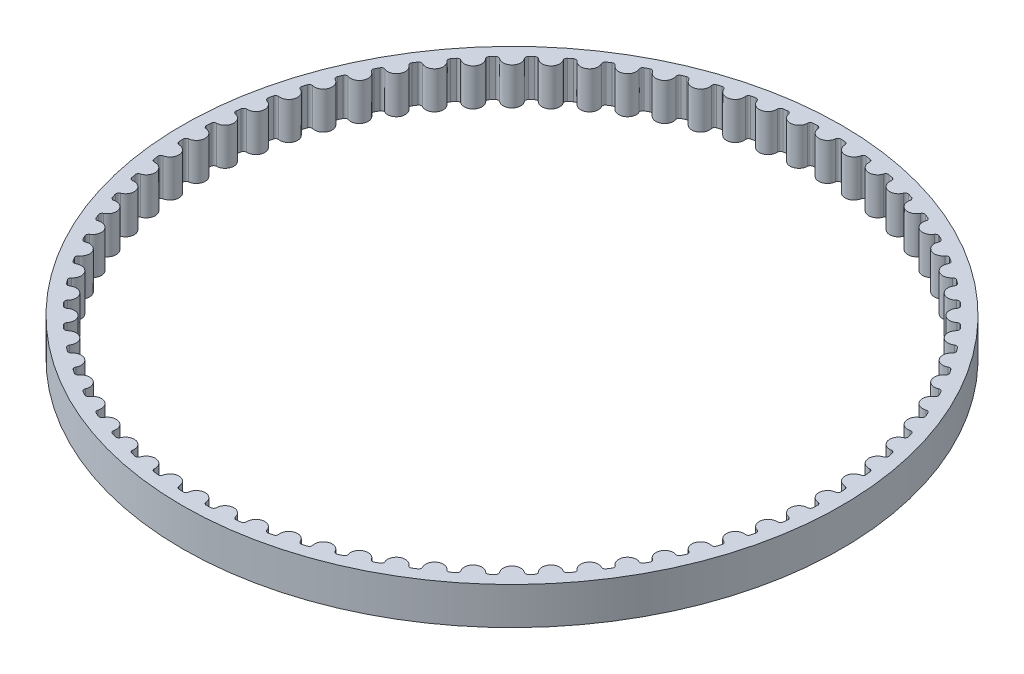
SolidWorks part; units mm, degrees
ref_plane "Front Plane" through (0, 0, 0) normal (0, 0, 1) x (1, 0, 0)
ref_plane "Top Plane" through (0, 0, 0) normal (0, 1, 0) x (1, 0, 0)
ref_plane "Right Plane" through (0, 0, 0) normal (1, 0, 0) x (0, 0, -1)
sketch "Sketch1" plane through (0, 0, 0) normal (0, 1, 0) x (1, 0, 0)
  circle A0 centre (0, 0) radius 35.2965
  arc B0 (-1.7184, -33.953) -> (-1.2474, -33.9736) centre (0, 0) ccw
  arc B1 (-1.2474, -33.9736) -> (-0.9391, -33.7063) centre (-1.2364, -33.6748) ccw
  arc B2 (0.9391, -33.7063) -> (-0.9391, -33.7063) centre (0, -33.806) ccw
  arc B3 (0.9391, -33.7063) -> (1.2474, -33.9736) centre (1.2364, -33.6748) ccw
  arc B4 (1.2474, -33.9736) -> (1.7184, -33.953) centre (0, 0) ccw
  arc B5 (1.7184, -33.953) -> (2.0022, -33.6599) centre (1.7032, -33.6544) ccw
  arc B6 (3.8732, -33.4962) -> (2.0022, -33.6599) centre (2.9464, -33.6773) ccw
  arc B7 (3.8732, -33.4962) -> (4.2036, -33.7356) centre (4.1667, -33.4389) ccw
  arc B8 (4.2036, -33.7356) -> (4.671, -33.674) centre (0, 0) ccw
  arc B9 (4.671, -33.674) -> (4.9282, -33.3573) centre (4.6299, -33.3779) ccw
  arc B10 (6.7779, -33.0312) -> (4.9282, -33.3573) centre (5.8703, -33.2924) ccw
  arc B11 (6.7779, -33.0312) -> (7.1279, -33.2408) centre (7.0652, -32.9485) ccw
  arc B12 (7.1279, -33.2408) -> (7.5881, -33.1388) centre (0, 0) ccw
  arc B13 (7.5881, -33.1388) -> (7.8168, -32.8009) centre (7.5214, -32.8473) ccw
  arc B14 (9.6309, -32.3148) -> (7.8168, -32.8009) centre (8.7496, -32.6541) ccw
  arc B15 (9.6309, -32.3148) -> (9.9979, -32.4931) centre (9.9099, -32.2073) ccw
  arc B16 (9.9979, -32.4931) -> (10.4475, -32.3513) centre (0, 0) ccw
  arc B17 (10.4475, -32.3513) -> (10.6458, -31.9948) centre (10.3556, -32.0668) ccw
  arc B18 (12.4107, -31.3524) -> (10.6458, -31.9948) centre (11.5623, -31.7672) ccw
  arc B19 (12.4107, -31.3524) -> (12.7918, -31.4981) centre (12.6793, -31.2211) ccw
  arc B20 (12.7918, -31.4981) -> (13.2273, -31.3177) centre (0, 0) ccw
  arc B21 (13.2273, -31.3177) -> (13.3938, -30.9452) centre (13.111, -31.0422) ccw
  arc B22 (15.096, -30.1514) -> (13.3938, -30.9452) centre (14.287, -30.6386) ccw
  arc B23 (15.096, -30.1514) -> (15.4884, -30.2634) centre (15.3521, -29.9972) ccw
  arc B24 (15.4884, -30.2634) -> (15.9065, -30.0457) centre (0, 0) ccw
  arc B25 (15.9065, -30.0457) -> (16.0399, -29.6601) centre (15.7666, -29.7814) ccw
  arc B26 (17.6664, -28.721) -> (16.0399, -29.6601) centre (16.903, -29.2768) ccw
  arc B27 (17.6664, -28.721) -> (18.067, -28.7983) centre (17.9081, -28.545) ccw
  arc B28 (18.067, -28.7983) -> (18.4647, -28.545) centre (0, 0) ccw
  arc B29 (18.4647, -28.545) -> (18.5639, -28.1492) centre (18.3023, -28.2939) ccw
  arc B30 (20.1024, -27.072) -> (18.5639, -28.1492) centre (19.3903, -27.6922) ccw
  arc B31 (20.1024, -27.072) -> (20.5082, -27.1141) centre (20.3279, -26.8756) ccw
  arc B32 (20.5082, -27.1141) -> (20.8822, -26.8271) centre (0, 0) ccw
  arc B33 (20.8822, -26.8271) -> (20.9466, -26.4242) centre (20.6986, -26.5911) ccw
  arc B34 (22.3854, -25.2169) -> (20.9466, -26.4242) centre (21.7301, -25.8969) ccw
  arc B35 (22.3854, -25.2169) -> (22.7933, -25.2235) centre (22.5929, -25.0016) ccw
  arc B36 (22.7933, -25.2235) -> (23.1409, -24.905) centre (0, 0) ccw
  arc B37 (23.1409, -24.905) -> (23.1699, -24.498) centre (22.9374, -24.6859) ccw
  arc B38 (24.498, -23.1699) -> (23.1699, -24.498) centre (23.9044, -23.9044) ccw
  arc B39 (24.498, -23.1699) -> (24.905, -23.1409) centre (24.6859, -22.9374) ccw
  arc B40 (24.905, -23.1409) -> (25.2235, -22.7933) centre (0, 0) ccw
  arc B41 (25.2235, -22.7933) -> (25.2169, -22.3854) centre (25.0016, -22.5929) ccw
  arc B42 (26.4242, -20.9466) -> (25.2169, -22.3854) centre (25.8969, -21.7301) ccw
  arc B43 (26.4242, -20.9466) -> (26.8271, -20.8822) centre (26.5911, -20.6986) ccw
  arc B44 (26.8271, -20.8822) -> (27.1141, -20.5082) centre (0, 0) ccw
  arc B45 (27.1141, -20.5082) -> (27.072, -20.1024) centre (26.8756, -20.3279) ccw
  arc B46 (28.1492, -18.5639) -> (27.072, -20.1024) centre (27.6922, -19.3903) ccw
  arc B47 (28.1492, -18.5639) -> (28.545, -18.4647) centre (28.2939, -18.3023) ccw
  arc B48 (28.545, -18.4647) -> (28.7983, -18.067) centre (0, 0) ccw
  arc B49 (28.7983, -18.067) -> (28.721, -17.6664) centre (28.545, -17.9081) ccw
  arc B50 (29.6601, -16.0399) -> (28.721, -17.6664) centre (29.2768, -16.903) ccw
  arc B51 (29.6601, -16.0399) -> (30.0457, -15.9065) centre (29.7814, -15.7666) ccw
  arc B52 (30.0457, -15.9065) -> (30.2634, -15.4884) centre (0, 0) ccw
  arc B53 (30.2634, -15.4884) -> (30.1514, -15.096) centre (29.9972, -15.3521) ccw
  arc B54 (30.9452, -13.3938) -> (30.1514, -15.096) centre (30.6386, -14.287) ccw
  arc B55 (30.9452, -13.3938) -> (31.3177, -13.2273) centre (31.0422, -13.111) ccw
  arc B56 (31.3177, -13.2273) -> (31.4981, -12.7918) centre (0, 0) ccw
  arc B57 (31.4981, -12.7918) -> (31.3524, -12.4107) centre (31.2211, -12.6793) ccw
  arc B58 (31.9948, -10.6458) -> (31.3524, -12.4107) centre (31.7672, -11.5623) ccw
  arc B59 (31.9948, -10.6458) -> (32.3513, -10.4475) centre (32.0668, -10.3556) ccw
  arc B60 (32.3513, -10.4475) -> (32.4931, -9.9979) centre (0, 0) ccw
  arc B61 (32.4931, -9.9979) -> (32.3148, -9.6309) centre (32.2073, -9.9099) ccw
  arc B62 (32.8009, -7.8168) -> (32.3148, -9.6309) centre (32.6541, -8.7496) ccw
  arc B63 (32.8009, -7.8168) -> (33.1388, -7.5881) centre (32.8473, -7.5214) ccw
  arc B64 (33.1388, -7.5881) -> (33.2408, -7.1279) centre (0, 0) ccw
  arc B65 (33.2408, -7.1279) -> (33.0312, -6.7779) centre (32.9485, -7.0652) ccw
  arc B66 (33.3573, -4.9282) -> (33.0312, -6.7779) centre (33.2924, -5.8703) ccw
  arc B67 (33.3573, -4.9282) -> (33.674, -4.671) centre (33.3779, -4.6299) ccw
  arc B68 (33.674, -4.671) -> (33.7356, -4.2036) centre (0, 0) ccw
  arc B69 (33.7356, -4.2036) -> (33.4962, -3.8732) centre (33.4389, -4.1667) ccw
  arc B70 (33.6599, -2.0022) -> (33.4962, -3.8732) centre (33.6773, -2.9464) ccw
  arc B71 (33.6599, -2.0022) -> (33.953, -1.7184) centre (33.6544, -1.7032) ccw
  arc B72 (33.953, -1.7184) -> (33.9736, -1.2474) centre (0, 0) ccw
  arc B73 (33.9736, -1.2474) -> (33.7063, -0.9391) centre (33.6748, -1.2364) ccw
  arc B74 (33.7063, 0.9391) -> (33.7063, -0.9391) centre (33.806, 0) ccw
  arc B75 (33.7063, 0.9391) -> (33.9736, 1.2474) centre (33.6748, 1.2364) ccw
  arc B76 (33.9736, 1.2474) -> (33.953, 1.7184) centre (0, 0) ccw
  arc B77 (33.953, 1.7184) -> (33.6599, 2.0022) centre (33.6544, 1.7032) ccw
  arc B78 (33.4962, 3.8732) -> (33.6599, 2.0022) centre (33.6773, 2.9464) ccw
  arc B79 (33.4962, 3.8732) -> (33.7356, 4.2036) centre (33.4389, 4.1667) ccw
  arc B80 (33.7356, 4.2036) -> (33.674, 4.671) centre (0, 0) ccw
  arc B81 (33.674, 4.671) -> (33.3573, 4.9282) centre (33.3779, 4.6299) ccw
  arc B82 (33.0312, 6.7779) -> (33.3573, 4.9282) centre (33.2924, 5.8703) ccw
  arc B83 (33.0312, 6.7779) -> (33.2408, 7.1279) centre (32.9485, 7.0652) ccw
  arc B84 (33.2408, 7.1279) -> (33.1388, 7.5881) centre (0, 0) ccw
  arc B85 (33.1388, 7.5881) -> (32.8009, 7.8168) centre (32.8473, 7.5214) ccw
  arc B86 (32.3148, 9.6309) -> (32.8009, 7.8168) centre (32.6541, 8.7496) ccw
  arc B87 (32.3148, 9.6309) -> (32.4931, 9.9979) centre (32.2073, 9.9099) ccw
  arc B88 (32.4931, 9.9979) -> (32.3513, 10.4475) centre (0, 0) ccw
  arc B89 (32.3513, 10.4475) -> (31.9948, 10.6458) centre (32.0668, 10.3556) ccw
  arc B90 (31.3524, 12.4107) -> (31.9948, 10.6458) centre (31.7672, 11.5623) ccw
  arc B91 (31.3524, 12.4107) -> (31.4981, 12.7918) centre (31.2211, 12.6793) ccw
  arc B92 (31.4981, 12.7918) -> (31.3177, 13.2273) centre (0, 0) ccw
  arc B93 (31.3177, 13.2273) -> (30.9452, 13.3938) centre (31.0422, 13.111) ccw
  arc B94 (30.1514, 15.096) -> (30.9452, 13.3938) centre (30.6386, 14.287) ccw
  arc B95 (30.1514, 15.096) -> (30.2634, 15.4884) centre (29.9972, 15.3521) ccw
  arc B96 (30.2634, 15.4884) -> (30.0457, 15.9065) centre (0, 0) ccw
  arc B97 (30.0457, 15.9065) -> (29.6601, 16.0399) centre (29.7814, 15.7666) ccw
  arc B98 (28.721, 17.6664) -> (29.6601, 16.0399) centre (29.2768, 16.903) ccw
  arc B99 (28.721, 17.6664) -> (28.7983, 18.067) centre (28.545, 17.9081) ccw
  arc B100 (28.7983, 18.067) -> (28.545, 18.4647) centre (0, 0) ccw
  arc B101 (28.545, 18.4647) -> (28.1492, 18.5639) centre (28.2939, 18.3023) ccw
  arc B102 (27.072, 20.1024) -> (28.1492, 18.5639) centre (27.6922, 19.3903) ccw
  arc B103 (27.072, 20.1024) -> (27.1141, 20.5082) centre (26.8756, 20.3279) ccw
  arc B104 (27.1141, 20.5082) -> (26.8271, 20.8822) centre (0, 0) ccw
  arc B105 (26.8271, 20.8822) -> (26.4242, 20.9466) centre (26.5911, 20.6986) ccw
  arc B106 (25.2169, 22.3854) -> (26.4242, 20.9466) centre (25.8969, 21.7301) ccw
  arc B107 (25.2169, 22.3854) -> (25.2235, 22.7933) centre (25.0016, 22.5929) ccw
  arc B108 (25.2235, 22.7933) -> (24.905, 23.1409) centre (0, 0) ccw
  arc B109 (24.905, 23.1409) -> (24.498, 23.1699) centre (24.6859, 22.9374) ccw
  arc B110 (23.1699, 24.498) -> (24.498, 23.1699) centre (23.9044, 23.9044) ccw
  arc B111 (23.1699, 24.498) -> (23.1409, 24.905) centre (22.9374, 24.6859) ccw
  arc B112 (23.1409, 24.905) -> (22.7933, 25.2235) centre (0, 0) ccw
  arc B113 (22.7933, 25.2235) -> (22.3854, 25.2169) centre (22.5929, 25.0016) ccw
  arc B114 (20.9466, 26.4242) -> (22.3854, 25.2169) centre (21.7301, 25.8969) ccw
  arc B115 (20.9466, 26.4242) -> (20.8822, 26.8271) centre (20.6986, 26.5911) ccw
  arc B116 (20.8822, 26.8271) -> (20.5082, 27.1141) centre (0, 0) ccw
  arc B117 (20.5082, 27.1141) -> (20.1024, 27.072) centre (20.3279, 26.8756) ccw
  arc B118 (18.5639, 28.1492) -> (20.1024, 27.072) centre (19.3903, 27.6922) ccw
  arc B119 (18.5639, 28.1492) -> (18.4647, 28.545) centre (18.3023, 28.2939) ccw
  arc B120 (18.4647, 28.545) -> (18.067, 28.7983) centre (0, 0) ccw
  arc B121 (18.067, 28.7983) -> (17.6664, 28.721) centre (17.9081, 28.545) ccw
  arc B122 (16.0399, 29.6601) -> (17.6664, 28.721) centre (16.903, 29.2768) ccw
  arc B123 (16.0399, 29.6601) -> (15.9065, 30.0457) centre (15.7666, 29.7814) ccw
  arc B124 (15.9065, 30.0457) -> (15.4884, 30.2634) centre (0, 0) ccw
  arc B125 (15.4884, 30.2634) -> (15.096, 30.1514) centre (15.3521, 29.9972) ccw
  arc B126 (13.3938, 30.9452) -> (15.096, 30.1514) centre (14.287, 30.6386) ccw
  arc B127 (13.3938, 30.9452) -> (13.2273, 31.3177) centre (13.111, 31.0422) ccw
  arc B128 (13.2273, 31.3177) -> (12.7918, 31.4981) centre (0, 0) ccw
  arc B129 (12.7918, 31.4981) -> (12.4107, 31.3524) centre (12.6793, 31.2211) ccw
  arc B130 (10.6458, 31.9948) -> (12.4107, 31.3524) centre (11.5623, 31.7672) ccw
  arc B131 (10.6458, 31.9948) -> (10.4475, 32.3513) centre (10.3556, 32.0668) ccw
  arc B132 (10.4475, 32.3513) -> (9.9979, 32.4931) centre (0, 0) ccw
  arc B133 (9.9979, 32.4931) -> (9.6309, 32.3148) centre (9.9099, 32.2073) ccw
  arc B134 (7.8168, 32.8009) -> (9.6309, 32.3148) centre (8.7496, 32.6541) ccw
  arc B135 (7.8168, 32.8009) -> (7.5881, 33.1388) centre (7.5214, 32.8473) ccw
  arc B136 (7.5881, 33.1388) -> (7.1279, 33.2408) centre (0, 0) ccw
  arc B137 (7.1279, 33.2408) -> (6.7779, 33.0312) centre (7.0652, 32.9485) ccw
  arc B138 (4.9282, 33.3573) -> (6.7779, 33.0312) centre (5.8703, 33.2924) ccw
  arc B139 (4.9282, 33.3573) -> (4.671, 33.674) centre (4.6299, 33.3779) ccw
  arc B140 (4.671, 33.674) -> (4.2036, 33.7356) centre (0, 0) ccw
  arc B141 (4.2036, 33.7356) -> (3.8732, 33.4962) centre (4.1667, 33.4389) ccw
  arc B142 (2.0022, 33.6599) -> (3.8732, 33.4962) centre (2.9464, 33.6773) ccw
  arc B143 (2.0022, 33.6599) -> (1.7184, 33.953) centre (1.7032, 33.6544) ccw
  arc B144 (1.7184, 33.953) -> (1.2474, 33.9736) centre (0, 0) ccw
  arc B145 (1.2474, 33.9736) -> (0.9391, 33.7063) centre (1.2364, 33.6748) ccw
  arc B146 (-0.9391, 33.7063) -> (0.9391, 33.7063) centre (0, 33.806) ccw
  arc B147 (-0.9391, 33.7063) -> (-1.2474, 33.9736) centre (-1.2364, 33.6748) ccw
  arc B148 (-1.2474, 33.9736) -> (-1.7184, 33.953) centre (0, 0) ccw
  arc B149 (-1.7184, 33.953) -> (-2.0022, 33.6599) centre (-1.7032, 33.6544) ccw
  arc B150 (-3.8732, 33.4962) -> (-2.0022, 33.6599) centre (-2.9464, 33.6773) ccw
  arc B151 (-3.8732, 33.4962) -> (-4.2036, 33.7356) centre (-4.1667, 33.4389) ccw
  arc B152 (-4.2036, 33.7356) -> (-4.671, 33.674) centre (0, 0) ccw
  arc B153 (-4.671, 33.674) -> (-4.9282, 33.3573) centre (-4.6299, 33.3779) ccw
  arc B154 (-6.7779, 33.0312) -> (-4.9282, 33.3573) centre (-5.8703, 33.2924) ccw
  arc B155 (-6.7779, 33.0312) -> (-7.1279, 33.2408) centre (-7.0652, 32.9485) ccw
  arc B156 (-7.1279, 33.2408) -> (-7.5881, 33.1388) centre (0, 0) ccw
  arc B157 (-7.5881, 33.1388) -> (-7.8168, 32.8009) centre (-7.5214, 32.8473) ccw
  arc B158 (-9.6309, 32.3148) -> (-7.8168, 32.8009) centre (-8.7496, 32.6541) ccw
  arc B159 (-9.6309, 32.3148) -> (-9.9979, 32.4931) centre (-9.9099, 32.2073) ccw
  arc B160 (-9.9979, 32.4931) -> (-10.4475, 32.3513) centre (0, 0) ccw
  arc B161 (-10.4475, 32.3513) -> (-10.6458, 31.9948) centre (-10.3556, 32.0668) ccw
  arc B162 (-12.4107, 31.3524) -> (-10.6458, 31.9948) centre (-11.5623, 31.7672) ccw
  arc B163 (-12.4107, 31.3524) -> (-12.7918, 31.4981) centre (-12.6793, 31.2211) ccw
  arc B164 (-12.7918, 31.4981) -> (-13.2273, 31.3177) centre (0, 0) ccw
  arc B165 (-13.2273, 31.3177) -> (-13.3938, 30.9452) centre (-13.111, 31.0422) ccw
  arc B166 (-15.096, 30.1514) -> (-13.3938, 30.9452) centre (-14.287, 30.6386) ccw
  arc B167 (-15.096, 30.1514) -> (-15.4884, 30.2634) centre (-15.3521, 29.9972) ccw
  arc B168 (-15.4884, 30.2634) -> (-15.9065, 30.0457) centre (0, 0) ccw
  arc B169 (-15.9065, 30.0457) -> (-16.0399, 29.6601) centre (-15.7666, 29.7814) ccw
  arc B170 (-17.6664, 28.721) -> (-16.0399, 29.6601) centre (-16.903, 29.2768) ccw
  arc B171 (-17.6664, 28.721) -> (-18.067, 28.7983) centre (-17.9081, 28.545) ccw
  arc B172 (-18.067, 28.7983) -> (-18.4647, 28.545) centre (0, 0) ccw
  arc B173 (-18.4647, 28.545) -> (-18.5639, 28.1492) centre (-18.3023, 28.2939) ccw
  arc B174 (-20.1024, 27.072) -> (-18.5639, 28.1492) centre (-19.3903, 27.6922) ccw
  arc B175 (-20.1024, 27.072) -> (-20.5082, 27.1141) centre (-20.3279, 26.8756) ccw
  arc B176 (-20.5082, 27.1141) -> (-20.8822, 26.8271) centre (0, 0) ccw
  arc B177 (-20.8822, 26.8271) -> (-20.9466, 26.4242) centre (-20.6986, 26.5911) ccw
  arc B178 (-22.3854, 25.2169) -> (-20.9466, 26.4242) centre (-21.7301, 25.8969) ccw
  arc B179 (-22.3854, 25.2169) -> (-22.7933, 25.2235) centre (-22.5929, 25.0016) ccw
  arc B180 (-22.7933, 25.2235) -> (-23.1409, 24.905) centre (0, 0) ccw
  arc B181 (-23.1409, 24.905) -> (-23.1699, 24.498) centre (-22.9374, 24.6859) ccw
  arc B182 (-24.498, 23.1699) -> (-23.1699, 24.498) centre (-23.9044, 23.9044) ccw
  arc B183 (-24.498, 23.1699) -> (-24.905, 23.1409) centre (-24.6859, 22.9374) ccw
  arc B184 (-24.905, 23.1409) -> (-25.2235, 22.7933) centre (0, 0) ccw
  arc B185 (-25.2235, 22.7933) -> (-25.2169, 22.3854) centre (-25.0016, 22.5929) ccw
  arc B186 (-26.4242, 20.9466) -> (-25.2169, 22.3854) centre (-25.8969, 21.7301) ccw
  arc B187 (-26.4242, 20.9466) -> (-26.8271, 20.8822) centre (-26.5911, 20.6986) ccw
  arc B188 (-26.8271, 20.8822) -> (-27.1141, 20.5082) centre (0, 0) ccw
  arc B189 (-27.1141, 20.5082) -> (-27.072, 20.1024) centre (-26.8756, 20.3279) ccw
  arc B190 (-28.1492, 18.5639) -> (-27.072, 20.1024) centre (-27.6922, 19.3903) ccw
  arc B191 (-28.1492, 18.5639) -> (-28.545, 18.4647) centre (-28.2939, 18.3023) ccw
  arc B192 (-28.545, 18.4647) -> (-28.7983, 18.067) centre (0, 0) ccw
  arc B193 (-28.7983, 18.067) -> (-28.721, 17.6664) centre (-28.545, 17.9081) ccw
  arc B194 (-29.6601, 16.0399) -> (-28.721, 17.6664) centre (-29.2768, 16.903) ccw
  arc B195 (-29.6601, 16.0399) -> (-30.0457, 15.9065) centre (-29.7814, 15.7666) ccw
  arc B196 (-30.0457, 15.9065) -> (-30.2634, 15.4884) centre (0, 0) ccw
  arc B197 (-30.2634, 15.4884) -> (-30.1514, 15.096) centre (-29.9972, 15.3521) ccw
  arc B198 (-30.9452, 13.3938) -> (-30.1514, 15.096) centre (-30.6386, 14.287) ccw
  arc B199 (-30.9452, 13.3938) -> (-31.3177, 13.2273) centre (-31.0422, 13.111) ccw
  arc B200 (-31.3177, 13.2273) -> (-31.4981, 12.7918) centre (0, 0) ccw
  arc B201 (-31.4981, 12.7918) -> (-31.3524, 12.4107) centre (-31.2211, 12.6793) ccw
  arc B202 (-31.9948, 10.6458) -> (-31.3524, 12.4107) centre (-31.7672, 11.5623) ccw
  arc B203 (-31.9948, 10.6458) -> (-32.3513, 10.4475) centre (-32.0668, 10.3556) ccw
  arc B204 (-32.3513, 10.4475) -> (-32.4931, 9.9979) centre (0, 0) ccw
  arc B205 (-32.4931, 9.9979) -> (-32.3148, 9.6309) centre (-32.2073, 9.9099) ccw
  arc B206 (-32.8009, 7.8168) -> (-32.3148, 9.6309) centre (-32.6541, 8.7496) ccw
  arc B207 (-32.8009, 7.8168) -> (-33.1388, 7.5881) centre (-32.8473, 7.5214) ccw
  arc B208 (-33.1388, 7.5881) -> (-33.2408, 7.1279) centre (0, 0) ccw
  arc B209 (-33.2408, 7.1279) -> (-33.0312, 6.7779) centre (-32.9485, 7.0652) ccw
  arc B210 (-33.3573, 4.9282) -> (-33.0312, 6.7779) centre (-33.2924, 5.8703) ccw
  arc B211 (-33.3573, 4.9282) -> (-33.674, 4.671) centre (-33.3779, 4.6299) ccw
  arc B212 (-33.674, 4.671) -> (-33.7356, 4.2036) centre (0, 0) ccw
  arc B213 (-33.7356, 4.2036) -> (-33.4962, 3.8732) centre (-33.4389, 4.1667) ccw
  arc B214 (-33.6599, 2.0022) -> (-33.4962, 3.8732) centre (-33.6773, 2.9464) ccw
  arc B215 (-33.6599, 2.0022) -> (-33.953, 1.7184) centre (-33.6544, 1.7032) ccw
  arc B216 (-33.953, 1.7184) -> (-33.9736, 1.2474) centre (0, 0) ccw
  arc B217 (-33.9736, 1.2474) -> (-33.7063, 0.9391) centre (-33.6748, 1.2364) ccw
  arc B218 (-33.7063, -0.9391) -> (-33.7063, 0.9391) centre (-33.806, 0) ccw
  arc B219 (-33.7063, -0.9391) -> (-33.9736, -1.2474) centre (-33.6748, -1.2364) ccw
  arc B220 (-33.9736, -1.2474) -> (-33.953, -1.7184) centre (0, 0) ccw
  arc B221 (-33.953, -1.7184) -> (-33.6599, -2.0022) centre (-33.6544, -1.7032) ccw
  arc B222 (-33.4962, -3.8732) -> (-33.6599, -2.0022) centre (-33.6773, -2.9464) ccw
  arc B223 (-33.4962, -3.8732) -> (-33.7356, -4.2036) centre (-33.4389, -4.1667) ccw
  arc B224 (-33.7356, -4.2036) -> (-33.674, -4.671) centre (0, 0) ccw
  arc B225 (-33.674, -4.671) -> (-33.3573, -4.9282) centre (-33.3779, -4.6299) ccw
  arc B226 (-33.0312, -6.7779) -> (-33.3573, -4.9282) centre (-33.2924, -5.8703) ccw
  arc B227 (-33.0312, -6.7779) -> (-33.2408, -7.1279) centre (-32.9485, -7.0652) ccw
  arc B228 (-33.2408, -7.1279) -> (-33.1388, -7.5881) centre (0, 0) ccw
  arc B229 (-33.1388, -7.5881) -> (-32.8009, -7.8168) centre (-32.8473, -7.5214) ccw
  arc B230 (-32.3148, -9.6309) -> (-32.8009, -7.8168) centre (-32.6541, -8.7496) ccw
  arc B231 (-32.3148, -9.6309) -> (-32.4931, -9.9979) centre (-32.2073, -9.9099) ccw
  arc B232 (-32.4931, -9.9979) -> (-32.3513, -10.4475) centre (0, 0) ccw
  arc B233 (-32.3513, -10.4475) -> (-31.9948, -10.6458) centre (-32.0668, -10.3556) ccw
  arc B234 (-31.3524, -12.4107) -> (-31.9948, -10.6458) centre (-31.7672, -11.5623) ccw
  arc B235 (-31.3524, -12.4107) -> (-31.4981, -12.7918) centre (-31.2211, -12.6793) ccw
  arc B236 (-31.4981, -12.7918) -> (-31.3177, -13.2273) centre (0, 0) ccw
  arc B237 (-31.3177, -13.2273) -> (-30.9452, -13.3938) centre (-31.0422, -13.111) ccw
  arc B238 (-30.1514, -15.096) -> (-30.9452, -13.3938) centre (-30.6386, -14.287) ccw
  arc B239 (-30.1514, -15.096) -> (-30.2634, -15.4884) centre (-29.9972, -15.3521) ccw
  arc B240 (-30.2634, -15.4884) -> (-30.0457, -15.9065) centre (0, 0) ccw
  arc B241 (-30.0457, -15.9065) -> (-29.6601, -16.0399) centre (-29.7814, -15.7666) ccw
  arc B242 (-28.721, -17.6664) -> (-29.6601, -16.0399) centre (-29.2768, -16.903) ccw
  arc B243 (-28.721, -17.6664) -> (-28.7983, -18.067) centre (-28.545, -17.9081) ccw
  arc B244 (-28.7983, -18.067) -> (-28.545, -18.4647) centre (0, 0) ccw
  arc B245 (-28.545, -18.4647) -> (-28.1492, -18.5639) centre (-28.2939, -18.3023) ccw
  arc B246 (-27.072, -20.1024) -> (-28.1492, -18.5639) centre (-27.6922, -19.3903) ccw
  arc B247 (-27.072, -20.1024) -> (-27.1141, -20.5082) centre (-26.8756, -20.3279) ccw
  arc B248 (-27.1141, -20.5082) -> (-26.8271, -20.8822) centre (0, 0) ccw
  arc B249 (-26.8271, -20.8822) -> (-26.4242, -20.9466) centre (-26.5911, -20.6986) ccw
  arc B250 (-25.2169, -22.3854) -> (-26.4242, -20.9466) centre (-25.8969, -21.7301) ccw
  arc B251 (-25.2169, -22.3854) -> (-25.2235, -22.7933) centre (-25.0016, -22.5929) ccw
  arc B252 (-25.2235, -22.7933) -> (-24.905, -23.1409) centre (0, 0) ccw
  arc B253 (-24.905, -23.1409) -> (-24.498, -23.1699) centre (-24.6859, -22.9374) ccw
  arc B254 (-23.1699, -24.498) -> (-24.498, -23.1699) centre (-23.9044, -23.9044) ccw
  arc B255 (-23.1699, -24.498) -> (-23.1409, -24.905) centre (-22.9374, -24.6859) ccw
  arc B256 (-23.1409, -24.905) -> (-22.7933, -25.2235) centre (0, 0) ccw
  arc B257 (-22.7933, -25.2235) -> (-22.3854, -25.2169) centre (-22.5929, -25.0016) ccw
  arc B258 (-20.9466, -26.4242) -> (-22.3854, -25.2169) centre (-21.7301, -25.8969) ccw
  arc B259 (-20.9466, -26.4242) -> (-20.8822, -26.8271) centre (-20.6986, -26.5911) ccw
  arc B260 (-20.8822, -26.8271) -> (-20.5082, -27.1141) centre (0, 0) ccw
  arc B261 (-20.5082, -27.1141) -> (-20.1024, -27.072) centre (-20.3279, -26.8756) ccw
  arc B262 (-18.5639, -28.1492) -> (-20.1024, -27.072) centre (-19.3903, -27.6922) ccw
  arc B263 (-18.5639, -28.1492) -> (-18.4647, -28.545) centre (-18.3023, -28.2939) ccw
  arc B264 (-18.4647, -28.545) -> (-18.067, -28.7983) centre (0, 0) ccw
  arc B265 (-18.067, -28.7983) -> (-17.6664, -28.721) centre (-17.9081, -28.545) ccw
  arc B266 (-16.0399, -29.6601) -> (-17.6664, -28.721) centre (-16.903, -29.2768) ccw
  arc B267 (-16.0399, -29.6601) -> (-15.9065, -30.0457) centre (-15.7666, -29.7814) ccw
  arc B268 (-15.9065, -30.0457) -> (-15.4884, -30.2634) centre (0, 0) ccw
  arc B269 (-15.4884, -30.2634) -> (-15.096, -30.1514) centre (-15.3521, -29.9972) ccw
  arc B270 (-13.3938, -30.9452) -> (-15.096, -30.1514) centre (-14.287, -30.6386) ccw
  arc B271 (-13.3938, -30.9452) -> (-13.2273, -31.3177) centre (-13.111, -31.0422) ccw
  arc B272 (-13.2273, -31.3177) -> (-12.7918, -31.4981) centre (0, 0) ccw
  arc B273 (-12.7918, -31.4981) -> (-12.4107, -31.3524) centre (-12.6793, -31.2211) ccw
  arc B274 (-10.6458, -31.9948) -> (-12.4107, -31.3524) centre (-11.5623, -31.7672) ccw
  arc B275 (-10.6458, -31.9948) -> (-10.4475, -32.3513) centre (-10.3556, -32.0668) ccw
  arc B276 (-10.4475, -32.3513) -> (-9.9979, -32.4931) centre (0, 0) ccw
  arc B277 (-9.9979, -32.4931) -> (-9.6309, -32.3148) centre (-9.9099, -32.2073) ccw
  arc B278 (-7.8168, -32.8009) -> (-9.6309, -32.3148) centre (-8.7496, -32.6541) ccw
  arc B279 (-7.8168, -32.8009) -> (-7.5881, -33.1388) centre (-7.5214, -32.8473) ccw
  arc B280 (-7.5881, -33.1388) -> (-7.1279, -33.2408) centre (0, 0) ccw
  arc B281 (-7.1279, -33.2408) -> (-6.7779, -33.0312) centre (-7.0652, -32.9485) ccw
  arc B282 (-4.9282, -33.3573) -> (-6.7779, -33.0312) centre (-5.8703, -33.2924) ccw
  arc B283 (-4.9282, -33.3573) -> (-4.671, -33.674) centre (-4.6299, -33.3779) ccw
  arc B284 (-4.671, -33.674) -> (-4.2036, -33.7356) centre (0, 0) ccw
  arc B285 (-4.2036, -33.7356) -> (-3.8732, -33.4962) centre (-4.1667, -33.4389) ccw
  arc B286 (-2.0022, -33.6599) -> (-3.8732, -33.4962) centre (-2.9464, -33.6773) ccw
  arc B287 (-2.0022, -33.6599) -> (-1.7184, -33.953) centre (-1.7032, -33.6544) ccw
  dimension "D1" = 1.3
sketch_block_instance "Block-72T GT2 Pulley-1"
sketch_block "Block-72T GT2 Pulley"
extrude "Boss-Extrude1" add sketch "Sketch1" along normal blind 4
